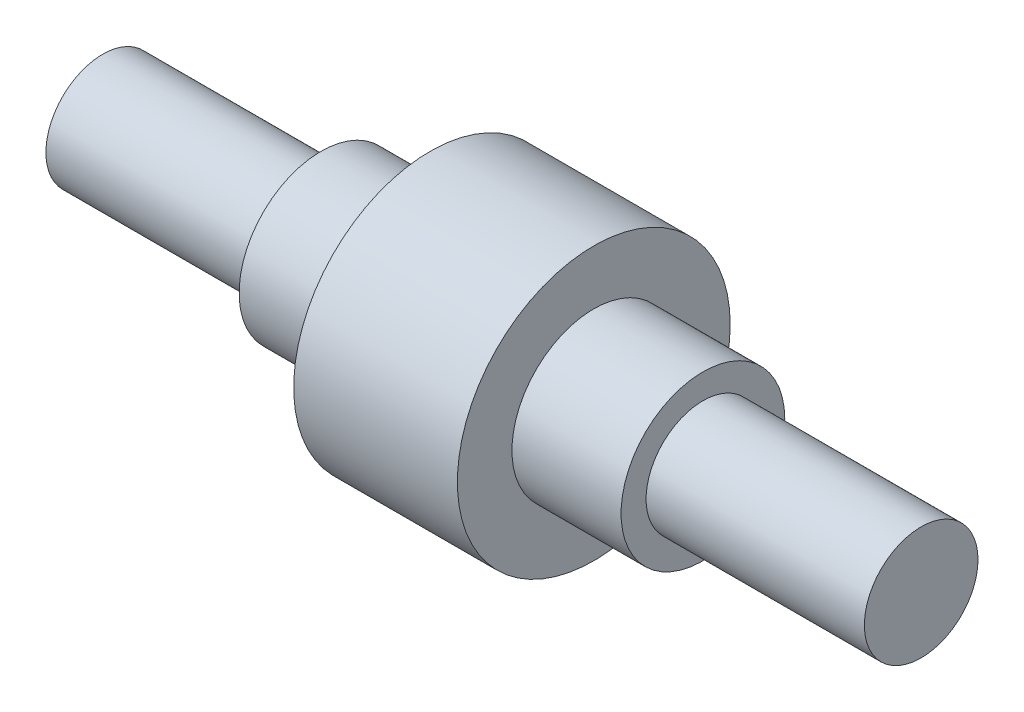
SolidWorks part; units mm, degrees
ref_plane "Front Plane" through (0, 0, 0) normal (0, 0, 1) x (1, 0, 0)
ref_plane "Top Plane" through (0, 0, 0) normal (0, 1, 0) x (1, 0, 0)
ref_plane "Right Plane" through (0, 0, 0) normal (1, 0, 0) x (0, 0, -1)
sketch "Sketch1" plane through (0, 0, 0) normal (0, 0, 1) x (1, 0, 0)
  line L0 (0, 0) -> (-222.8088, 0) construction
  line L1 (-30, -50) -> (30, -50)
  line L2 (30, -50) -> (30, -30)
  line L3 (-150, 0) -> (150, 0)
  line L4 (30, -30) -> (70, -30)
  line L5 (70, -30) -> (70, -20.8256)
  line L8 (150, 0) -> (150, -20.8256)
  line L9 (70, -20.8256) -> (150, -20.8256)
  line L10 (0, 0) -> (0, -98.7097) construction
  line L11 (-70, -20.8256) -> (-150, -20.8256)
  line L12 (-150, 0) -> (-150, -20.8256)
  line L15 (-70, -30) -> (-70, -20.8256)
  line L16 (-30, -30) -> (-70, -30)
  line L17 (-30, -50) -> (-30, -30)
  point P22 (0, -50)
  dimension "D1" = 80
  dimension "D2" = 40
  dimension "D3" = 30
revolve "Revolve6" add sketch "Sketch1" angle 360 about L0
